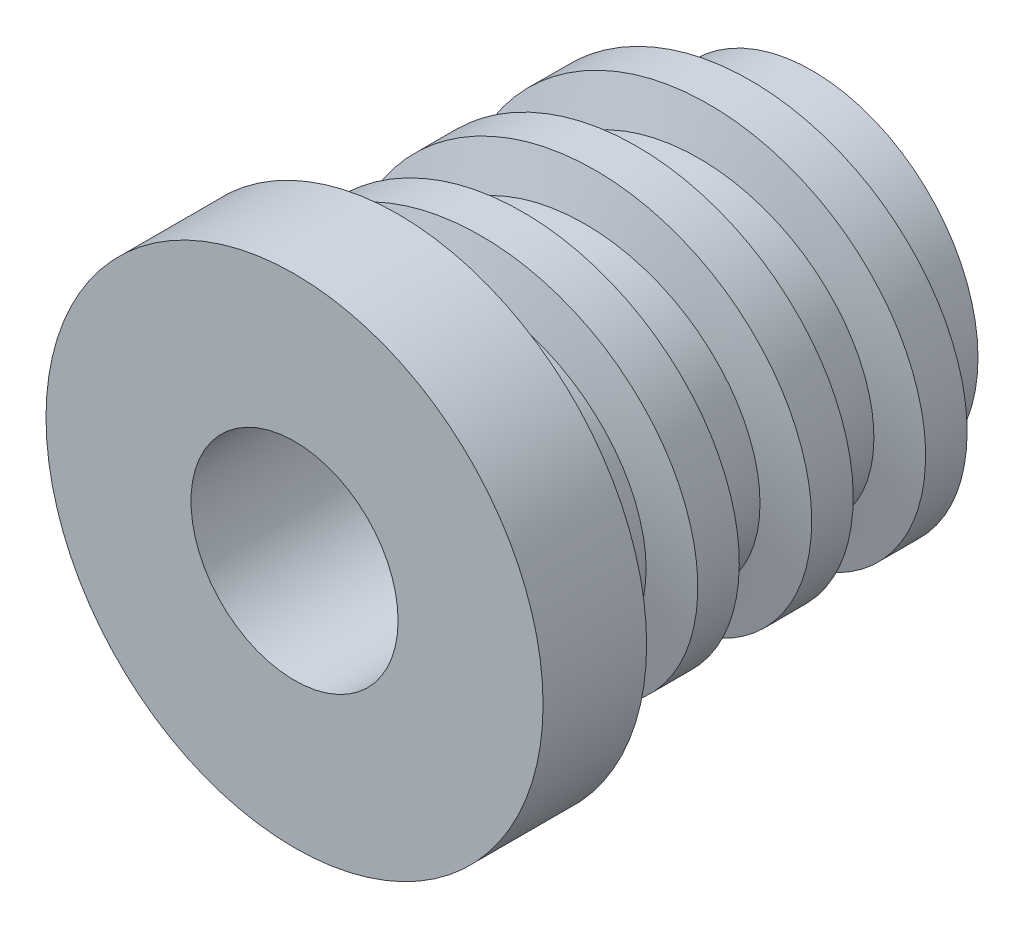
SolidWorks part; units mm, degrees
ref_plane "前视基准面" through (0, 0, 0) normal (0, 0, 1) x (1, 0, 0)
ref_plane "上视基准面" through (0, 0, 0) normal (0, 1, 0) x (1, 0, 0)
ref_plane "右视基准面" through (0, 0, 0) normal (1, 0, 0) x (0, 0, -1)
sketch "草图5" plane through (0, 0, 0) normal (0, 0, 1) x (1, 0, 0)
  circle A0 centre (0, 0) radius 8
extrude "凸台-拉伸3" add sketch "草图5" along normal blind 20
sketch "草图6" plane through (0, 0, 0) normal (0, 0, 1) x (1, 0, 0)
  circle A0 centre (0, 0) radius 8
curve "螺旋线/涡状线2" pitch 5.5 height 22 turns 4
ref_plane "基准面3" through (0, 0, 20) normal (0, 0, 1) x (1, 0, 0)
sketch "草图7" plane through (0, 0, 20) normal (0, 0, 1) x (1, 0, 0)
  circle A0 centre (0, 0) radius 12
extrude "凸台-拉伸4" add sketch "草图7" along normal blind 5
ref_plane "基准面4" through (-5.6569, -5.6569, 0) normal (0.7029, -0.7029, 0.1088) x (0.0769, -0.0769, -0.9941)
sketch "草图8" plane through (-5.6569, -5.6569, 0) normal (0.7029, -0.7029, 0.1088) x (0.0769, -0.0769, -0.9941)
  line L0 (0, 0) -> (-3, 0)
  line L1 (-0.5, -2) -> (-2.5, -2)
  line L2 (0, 0) -> (-0.5, -2)
  line L3 (-3, 0) -> (-2.5, -2)
  line L4 (-2.5, -2) -> (-2.5211, -2.025)
sweep "扫描2" add profiles "草图8" path "螺旋线/涡状线2"
ref_plane "基准面5" through (0, 0, 25) normal (0, 0, 1) x (1, 0, 0)
sketch "草图9" plane through (0, 0, 25) normal (0, 0, 1) x (1, 0, 0)
  circle A0 centre (0, 0) radius 5
extrude "切除-拉伸1" cut sketch "草图9" against normal blind 35 and the other way blind 5
